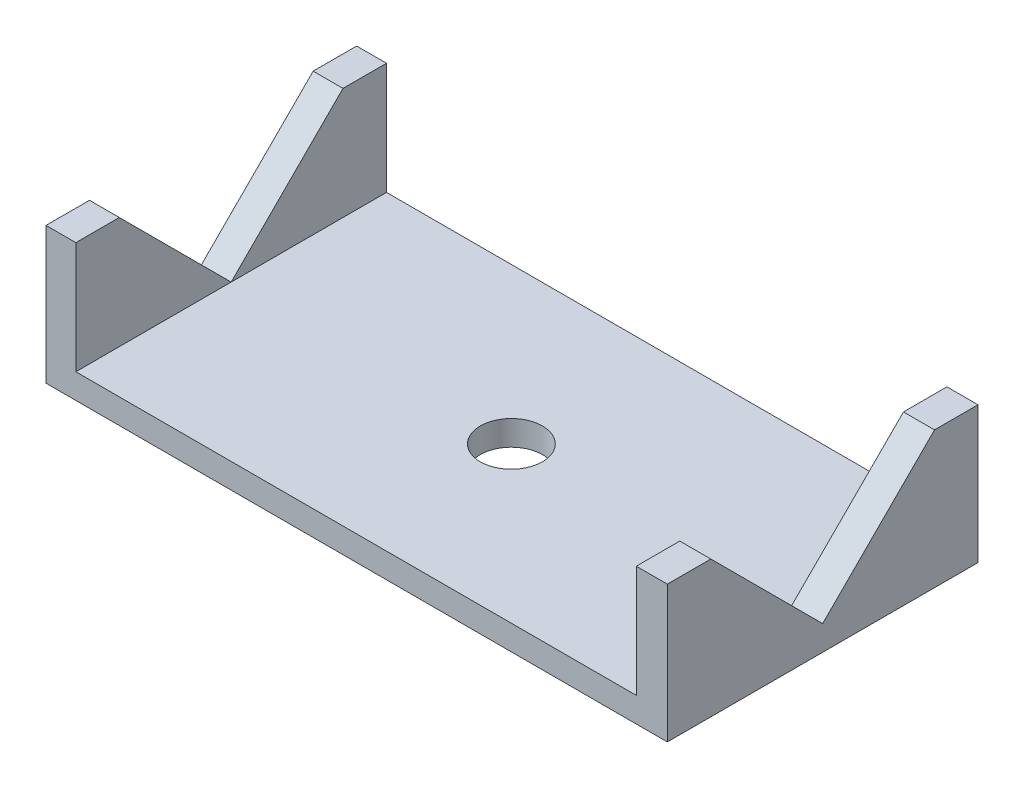
SolidWorks part; units mm, degrees
ref_plane "Front Plane" through (0, 0, 0) normal (0, 0, 1) x (1, 0, 0)
ref_plane "Top Plane" through (0, 0, 0) normal (0, 1, 0) x (1, 0, 0)
ref_plane "Right Plane" through (0, 0, 0) normal (1, 0, 0) x (0, 0, -1)
sketch "Sketch1" plane through (0, 0, 0) normal (0, 1, 0) x (1, 0, 0)
  line L1 (-25, -12.5) -> (25, -12.5)
  line L2 (-25, -12.5) -> (-25, 12.5)
  line L3 (-25, 12.5) -> (25, 12.5)
  line L4 (25, -12.5) -> (25, 12.5)
  line L5 (-25, -12.5) -> (25, 12.5) construction
  line L6 (-25, 12.5) -> (25, -12.5) construction
  point P0 (0, 0)
  dimension "D1" = 50
  dimension "D2" = 25
extrude "Boss-Extrude1" add sketch "Sketch1" along normal blind 2
sketch "Sketch2" plane through (0, 2, 0) normal (0, 1, 0) x (1, 0, 0)
  line L0 (25, 12.5) -> (-25, 12.5) construction
  line L1 (-25, -12.5) -> (-22.6, -12.5)
  line L2 (-25, -12.5) -> (-25, 12.5)
  line L3 (-25, 12.5) -> (-22.6, 12.5)
  line L4 (-22.6, -12.5) -> (-22.6, 12.5)
  dimension "D1" = 2.4
extrude "Boss-Extrude2" add sketch "Sketch2" along normal blind 9
sketch "Sketch3" plane through (-22.6, 0, 0) normal (1, 0, 0) x (0, 0, -1)
  line L0 (0, 11) -> (0, -1.6936) construction
  line L1 (-12.5, 11) -> (12.5, 11) construction
  line L2 (-9, 11) -> (0, 2)
  line L3 (-12.5, 2) -> (12.5, 2) construction
  line L4 (0, 2) -> (9, 11)
  line L5 (-9, 11) -> (9, 11)
  dimension "D1" = 45
  dimension "D2" = 45
extrude "Cut-Extrude1" cut sketch "Sketch3" against normal blind 9
sketch "Sketch4" plane through (0, 2, 0) normal (0, 1, 0) x (1, 0, 0)
  line L0 (25, 12.5) -> (-22.6, 12.5) construction
  line L1 (25, -12.5) -> (22.5, -12.5)
  line L2 (25, -12.5) -> (25, 12.5)
  line L3 (25, 12.5) -> (22.5, 12.5)
  line L4 (22.5, -12.5) -> (22.5, 12.5)
  dimension "D1" = 2.5
extrude "Boss-Extrude3" add sketch "Sketch4" along normal blind 9
sketch "Sketch5" plane through (22.5, 0, 0) normal (-1, 0, 0) x (0, 0, 1)
  line L0 (0, 11) -> (0, 0.6682) construction
  line L1 (-12.5, 11) -> (12.5, 11) construction
  line L2 (0, 2) -> (-9, 11)
  line L3 (-12.5, 2) -> (12.5, 2) construction
  line L4 (-9, 11) -> (9, 11)
  line L5 (9, 11) -> (0, 2)
  dimension "D1" = 45
  dimension "D2" = 45
extrude "Cut-Extrude2" cut sketch "Sketch5" against normal blind 9
sketch "Sketch6" plane through (0, 2, 0) normal (0, 1, 0) x (1, 0, 0)
  line L0 (-0.05, 12.5) -> (-0.05, -12.5) construction
  line L1 (22.5, 12.5) -> (-22.6, 12.5) construction
  line L2 (-22.6, -12.5) -> (22.5, -12.5) construction
  circle A0 centre (-0.05, 0) radius 2.5
  dimension "D1" = 5
  dimension "D2" = 12.5
extrude "Cut-Extrude4" cut sketch "Sketch6" against normal through all contours A0
